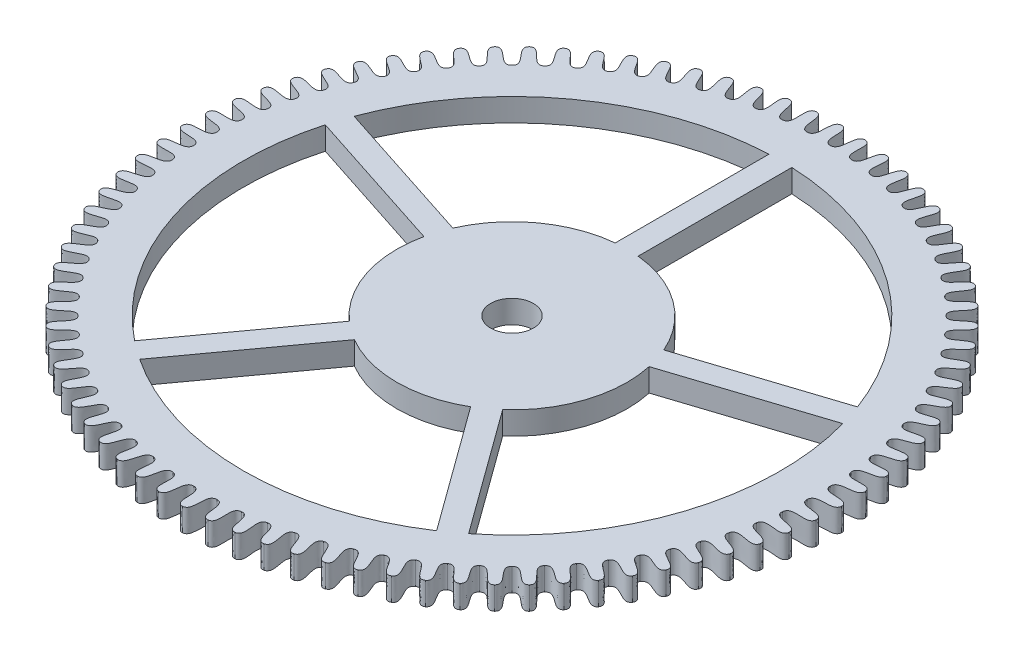
SolidWorks part; units mm, degrees
ref_plane "Alzado" through (0, 0, 0) normal (0, 0, 1) x (1, 0, 0)
ref_plane "Planta" through (0, 0, 0) normal (0, 1, 0) x (1, 0, 0)
ref_plane "Vista lateral" through (0, 0, 0) normal (1, 0, 0) x (0, 0, -1)
sketch "Sketch1" plane through (0, 0, 0) normal (0, 1, 0) x (1, 0, 0)
  line L0 (0, -1000) -> (0, 49000) construction
  line L1 (0, 0) -> (1869.5597, 49965.0352) construction
  circle A0 centre (0, 0) radius 4.315 construction
  circle A1 centre (0, 0) radius 4.015 construction
  spline S0 degree 3 poles (0, 4.315) (0.1353, 4.3129) (0.008, 4.0167) (0.1501, 4.0122) knots 0 0 0 0 1 1 1 1
  spline S1 degree 3 poles (0, 4.315) (-0.1353, 4.3129) (-0.008, 4.0167) (-0.1501, 4.0122) knots 0 0 0 0 1 1 1 1
  spline S2 degree 3 poles (0.3225, 4.3029) (0.4572, 4.2907) (0.3081, 4.0048) (0.4495, 3.9898) knots 0 0 0 0 1 1 1 1
  spline S3 degree 3 poles (0.3225, 4.3029) (0.1874, 4.3109) (0.2922, 4.006) (0.1501, 4.0122) knots 0 0 0 0 1 1 1 1
  spline S4 degree 3 poles (0.6431, 4.2668) (0.7765, 4.2445) (0.6066, 3.9706) (0.7464, 3.945) knots 0 0 0 0 1 1 1 1
  spline S5 degree 3 poles (0.6431, 4.2668) (0.5091, 4.2849) (0.5907, 3.973) (0.4495, 3.9898) knots 0 0 0 0 1 1 1 1
  spline S6 degree 3 poles (0.9602, 4.2068) (1.0916, 4.1746) (0.9016, 3.9142) (1.0392, 3.8782) knots 0 0 0 0 1 1 1 1
  spline S7 degree 3 poles (0.9602, 4.2068) (0.8278, 4.2348) (0.886, 3.9177) (0.7464, 3.945) knots 0 0 0 0 1 1 1 1
  spline S8 degree 3 poles (1.2719, 4.1233) (1.4005, 4.0814) (1.1916, 3.8358) (1.3261, 3.7897) knots 0 0 0 0 1 1 1 1
  spline S9 degree 3 poles (1.2719, 4.1233) (1.142, 4.1611) (1.1763, 3.8406) (1.0392, 3.8782) knots 0 0 0 0 1 1 1 1
  spline S10 degree 3 poles (1.5764, 4.0167) (1.7016, 3.9653) (1.4749, 3.7361) (1.6056, 3.68) knots 0 0 0 0 1 1 1 1
  spline S11 degree 3 poles (1.5764, 4.0167) (1.4498, 4.0642) (1.46, 3.7419) (1.3261, 3.7897) knots 0 0 0 0 1 1 1 1
  spline S12 degree 3 poles (1.8722, 3.8877) (1.9932, 3.8271) (1.75, 3.6154) (1.8761, 3.5497) knots 0 0 0 0 1 1 1 1
  spline S13 degree 3 poles (1.8722, 3.8877) (1.7494, 3.9445) (1.7356, 3.6223) (1.6056, 3.68) knots 0 0 0 0 1 1 1 1
  spline S14 degree 3 poles (2.1575, 3.7369) (2.2736, 3.6674) (2.0153, 3.4745) (2.1361, 3.3996) knots 0 0 0 0 1 1 1 1
  spline S15 degree 3 poles (2.1575, 3.7369) (2.0393, 3.8027) (2.0014, 3.4825) (1.8761, 3.5497) knots 0 0 0 0 1 1 1 1
  spline S16 degree 3 poles (2.4307, 3.5652) (2.5413, 3.4873) (2.2693, 3.3142) (2.3842, 3.2305) knots 0 0 0 0 1 1 1 1
  spline S17 degree 3 poles (2.4307, 3.5652) (2.3178, 3.6397) (2.2561, 3.3232) (2.1361, 3.3996) knots 0 0 0 0 1 1 1 1
  spline S18 degree 3 poles (2.6904, 3.3736) (2.7948, 3.2876) (2.5106, 3.1354) (2.6189, 3.0433) knots 0 0 0 0 1 1 1 1
  spline S19 degree 3 poles (2.6904, 3.3736) (2.5833, 3.4563) (2.4981, 3.1453) (2.3842, 3.2305) knots 0 0 0 0 1 1 1 1
  spline S20 degree 3 poles (2.9349, 3.1631) (3.0327, 3.0696) (2.7379, 2.939) (2.839, 2.839) knots 0 0 0 0 1 1 1 1
  spline S21 degree 3 poles (2.9349, 3.1631) (2.8344, 3.2536) (2.7262, 2.9499) (2.6189, 3.0433) knots 0 0 0 0 1 1 1 1
  spline S22 degree 3 poles (3.1631, 2.9349) (3.2536, 2.8344) (2.9499, 2.7262) (3.0433, 2.6189) knots 0 0 0 0 1 1 1 1
  spline S23 degree 3 poles (3.1631, 2.9349) (3.0696, 3.0327) (2.939, 2.7379) (2.839, 2.839) knots 0 0 0 0 1 1 1 1
  spline S24 degree 3 poles (3.3736, 2.6904) (3.4563, 2.5833) (3.1453, 2.4981) (3.2305, 2.3842) knots 0 0 0 0 1 1 1 1
  spline S25 degree 3 poles (3.3736, 2.6904) (3.2876, 2.7948) (3.1354, 2.5106) (3.0433, 2.6189) knots 0 0 0 0 1 1 1 1
  spline S26 degree 3 poles (3.5652, 2.4307) (3.6397, 2.3178) (3.3232, 2.2561) (3.3996, 2.1361) knots 0 0 0 0 1 1 1 1
  spline S27 degree 3 poles (3.5652, 2.4307) (3.4873, 2.5413) (3.3142, 2.2693) (3.2305, 2.3842) knots 0 0 0 0 1 1 1 1
  spline S28 degree 3 poles (3.7369, 2.1575) (3.8027, 2.0393) (3.4825, 2.0014) (3.5497, 1.8761) knots 0 0 0 0 1 1 1 1
  spline S29 degree 3 poles (3.7369, 2.1575) (3.6674, 2.2736) (3.4745, 2.0153) (3.3996, 2.1361) knots 0 0 0 0 1 1 1 1
  spline S30 degree 3 poles (3.8877, 1.8722) (3.9445, 1.7494) (3.6223, 1.7356) (3.68, 1.6056) knots 0 0 0 0 1 1 1 1
  spline S31 degree 3 poles (3.8877, 1.8722) (3.8271, 1.9932) (3.6154, 1.75) (3.5497, 1.8761) knots 0 0 0 0 1 1 1 1
  spline S32 degree 3 poles (4.0167, 1.5764) (4.0642, 1.4498) (3.7419, 1.46) (3.7897, 1.3261) knots 0 0 0 0 1 1 1 1
  spline S33 degree 3 poles (4.0167, 1.5764) (3.9653, 1.7016) (3.7361, 1.4749) (3.68, 1.6056) knots 0 0 0 0 1 1 1 1
  spline S34 degree 3 poles (4.1233, 1.2719) (4.1611, 1.142) (3.8406, 1.1763) (3.8782, 1.0392) knots 0 0 0 0 1 1 1 1
  spline S35 degree 3 poles (4.1233, 1.2719) (4.0814, 1.4005) (3.8358, 1.1916) (3.7897, 1.3261) knots 0 0 0 0 1 1 1 1
  spline S36 degree 3 poles (4.2068, 0.9602) (4.2348, 0.8278) (3.9177, 0.886) (3.945, 0.7464) knots 0 0 0 0 1 1 1 1
  spline S37 degree 3 poles (4.2068, 0.9602) (4.1746, 1.0916) (3.9142, 0.9016) (3.8782, 1.0392) knots 0 0 0 0 1 1 1 1
  spline S38 degree 3 poles (4.2668, 0.6431) (4.2849, 0.5091) (3.973, 0.5907) (3.9898, 0.4495) knots 0 0 0 0 1 1 1 1
  spline S39 degree 3 poles (4.2668, 0.6431) (4.2445, 0.7765) (3.9706, 0.6066) (3.945, 0.7464) knots 0 0 0 0 1 1 1 1
  spline S40 degree 3 poles (4.3029, 0.3225) (4.3109, 0.1874) (4.006, 0.2922) (4.0122, 0.1501) knots 0 0 0 0 1 1 1 1
  spline S41 degree 3 poles (4.3029, 0.3225) (4.2907, 0.4572) (4.0048, 0.3081) (3.9898, 0.4495) knots 0 0 0 0 1 1 1 1
  spline S42 degree 3 poles (4.315, 0) (4.3129, -0.1353) (4.0167, -0.008) (4.0122, -0.1501) knots 0 0 0 0 1 1 1 1
  spline S43 degree 3 poles (4.315, 0) (4.3129, 0.1353) (4.0167, 0.008) (4.0122, 0.1501) knots 0 0 0 0 1 1 1 1
  spline S44 degree 3 poles (4.3029, -0.3225) (4.2907, -0.4572) (4.0048, -0.3081) (3.9898, -0.4495) knots 0 0 0 0 1 1 1 1
  spline S45 degree 3 poles (4.3029, -0.3225) (4.3109, -0.1874) (4.006, -0.2922) (4.0122, -0.1501) knots 0 0 0 0 1 1 1 1
  spline S46 degree 3 poles (4.2668, -0.6431) (4.2445, -0.7765) (3.9706, -0.6066) (3.945, -0.7464) knots 0 0 0 0 1 1 1 1
  spline S47 degree 3 poles (4.2668, -0.6431) (4.2849, -0.5091) (3.973, -0.5907) (3.9898, -0.4495) knots 0 0 0 0 1 1 1 1
  spline S48 degree 3 poles (4.2068, -0.9602) (4.1746, -1.0916) (3.9142, -0.9016) (3.8782, -1.0392) knots 0 0 0 0 1 1 1 1
  spline S49 degree 3 poles (4.2068, -0.9602) (4.2348, -0.8278) (3.9177, -0.886) (3.945, -0.7464) knots 0 0 0 0 1 1 1 1
  spline S50 degree 3 poles (4.1233, -1.2719) (4.0814, -1.4005) (3.8358, -1.1916) (3.7897, -1.3261) knots 0 0 0 0 1 1 1 1
  spline S51 degree 3 poles (4.1233, -1.2719) (4.1611, -1.142) (3.8406, -1.1763) (3.8782, -1.0392) knots 0 0 0 0 1 1 1 1
  spline S52 degree 3 poles (4.0167, -1.5764) (3.9653, -1.7016) (3.7361, -1.4749) (3.68, -1.6056) knots 0 0 0 0 1 1 1 1
  spline S53 degree 3 poles (4.0167, -1.5764) (4.0642, -1.4498) (3.7419, -1.46) (3.7897, -1.3261) knots 0 0 0 0 1 1 1 1
  spline S54 degree 3 poles (3.8877, -1.8722) (3.8271, -1.9932) (3.6154, -1.75) (3.5497, -1.8761) knots 0 0 0 0 1 1 1 1
  spline S55 degree 3 poles (3.8877, -1.8722) (3.9445, -1.7494) (3.6223, -1.7356) (3.68, -1.6056) knots 0 0 0 0 1 1 1 1
  spline S56 degree 3 poles (3.7369, -2.1575) (3.6674, -2.2736) (3.4745, -2.0153) (3.3996, -2.1361) knots 0 0 0 0 1 1 1 1
  spline S57 degree 3 poles (3.7369, -2.1575) (3.8027, -2.0393) (3.4825, -2.0014) (3.5497, -1.8761) knots 0 0 0 0 1 1 1 1
  spline S58 degree 3 poles (3.5652, -2.4307) (3.4873, -2.5413) (3.3142, -2.2693) (3.2305, -2.3842) knots 0 0 0 0 1 1 1 1
  spline S59 degree 3 poles (3.5652, -2.4307) (3.6397, -2.3178) (3.3232, -2.2561) (3.3996, -2.1361) knots 0 0 0 0 1 1 1 1
  spline S60 degree 3 poles (3.3736, -2.6904) (3.2876, -2.7948) (3.1354, -2.5106) (3.0433, -2.6189) knots 0 0 0 0 1 1 1 1
  spline S61 degree 3 poles (3.3736, -2.6904) (3.4563, -2.5833) (3.1453, -2.4981) (3.2305, -2.3842) knots 0 0 0 0 1 1 1 1
  spline S62 degree 3 poles (3.1631, -2.9349) (3.0696, -3.0327) (2.939, -2.7379) (2.839, -2.839) knots 0 0 0 0 1 1 1 1
  spline S63 degree 3 poles (3.1631, -2.9349) (3.2536, -2.8344) (2.9499, -2.7262) (3.0433, -2.6189) knots 0 0 0 0 1 1 1 1
  spline S64 degree 3 poles (2.9349, -3.1631) (2.8344, -3.2536) (2.7262, -2.9499) (2.6189, -3.0433) knots 0 0 0 0 1 1 1 1
  spline S65 degree 3 poles (2.9349, -3.1631) (3.0327, -3.0696) (2.7379, -2.939) (2.839, -2.839) knots 0 0 0 0 1 1 1 1
  spline S66 degree 3 poles (2.6904, -3.3736) (2.5833, -3.4563) (2.4981, -3.1453) (2.3842, -3.2305) knots 0 0 0 0 1 1 1 1
  spline S67 degree 3 poles (2.6904, -3.3736) (2.7948, -3.2876) (2.5106, -3.1354) (2.6189, -3.0433) knots 0 0 0 0 1 1 1 1
  spline S68 degree 3 poles (2.4307, -3.5652) (2.3178, -3.6397) (2.2561, -3.3232) (2.1361, -3.3996) knots 0 0 0 0 1 1 1 1
  spline S69 degree 3 poles (2.4307, -3.5652) (2.5413, -3.4873) (2.2693, -3.3142) (2.3842, -3.2305) knots 0 0 0 0 1 1 1 1
  spline S70 degree 3 poles (2.1575, -3.7369) (2.0393, -3.8027) (2.0014, -3.4825) (1.8761, -3.5497) knots 0 0 0 0 1 1 1 1
  spline S71 degree 3 poles (2.1575, -3.7369) (2.2736, -3.6674) (2.0153, -3.4745) (2.1361, -3.3996) knots 0 0 0 0 1 1 1 1
  spline S72 degree 3 poles (1.8722, -3.8877) (1.7494, -3.9445) (1.7356, -3.6223) (1.6056, -3.68) knots 0 0 0 0 1 1 1 1
  spline S73 degree 3 poles (1.8722, -3.8877) (1.9932, -3.8271) (1.75, -3.6154) (1.8761, -3.5497) knots 0 0 0 0 1 1 1 1
  spline S74 degree 3 poles (1.5764, -4.0167) (1.4498, -4.0642) (1.46, -3.7419) (1.3261, -3.7897) knots 0 0 0 0 1 1 1 1
  spline S75 degree 3 poles (1.5764, -4.0167) (1.7016, -3.9653) (1.4749, -3.7361) (1.6056, -3.68) knots 0 0 0 0 1 1 1 1
  spline S76 degree 3 poles (1.2719, -4.1233) (1.142, -4.1611) (1.1763, -3.8406) (1.0392, -3.8782) knots 0 0 0 0 1 1 1 1
  spline S77 degree 3 poles (1.2719, -4.1233) (1.4005, -4.0814) (1.1916, -3.8358) (1.3261, -3.7897) knots 0 0 0 0 1 1 1 1
  spline S78 degree 3 poles (0.9602, -4.2068) (0.8278, -4.2348) (0.886, -3.9177) (0.7464, -3.945) knots 0 0 0 0 1 1 1 1
  spline S79 degree 3 poles (0.9602, -4.2068) (1.0916, -4.1746) (0.9016, -3.9142) (1.0392, -3.8782) knots 0 0 0 0 1 1 1 1
  spline S80 degree 3 poles (0.6431, -4.2668) (0.5091, -4.2849) (0.5907, -3.973) (0.4495, -3.9898) knots 0 0 0 0 1 1 1 1
  spline S81 degree 3 poles (0.6431, -4.2668) (0.7765, -4.2445) (0.6066, -3.9706) (0.7464, -3.945) knots 0 0 0 0 1 1 1 1
  spline S82 degree 3 poles (0.3225, -4.3029) (0.1874, -4.3109) (0.2922, -4.006) (0.1501, -4.0122) knots 0 0 0 0 1 1 1 1
  spline S83 degree 3 poles (0.3225, -4.3029) (0.4572, -4.2907) (0.3081, -4.0048) (0.4495, -3.9898) knots 0 0 0 0 1 1 1 1
  spline S84 degree 3 poles (0, -4.315) (-0.1353, -4.3129) (-0.008, -4.0167) (-0.1501, -4.0122) knots 0 0 0 0 1 1 1 1
  spline S85 degree 3 poles (0, -4.315) (0.1353, -4.3129) (0.008, -4.0167) (0.1501, -4.0122) knots 0 0 0 0 1 1 1 1
  spline S86 degree 3 poles (-0.3225, -4.3029) (-0.4572, -4.2907) (-0.3081, -4.0048) (-0.4495, -3.9898) knots 0 0 0 0 1 1 1 1
  spline S87 degree 3 poles (-0.3225, -4.3029) (-0.1874, -4.3109) (-0.2922, -4.006) (-0.1501, -4.0122) knots 0 0 0 0 1 1 1 1
  spline S88 degree 3 poles (-0.6431, -4.2668) (-0.7765, -4.2445) (-0.6066, -3.9706) (-0.7464, -3.945) knots 0 0 0 0 1 1 1 1
  spline S89 degree 3 poles (-0.6431, -4.2668) (-0.5091, -4.2849) (-0.5907, -3.973) (-0.4495, -3.9898) knots 0 0 0 0 1 1 1 1
  spline S90 degree 3 poles (-0.9602, -4.2068) (-1.0916, -4.1746) (-0.9016, -3.9142) (-1.0392, -3.8782) knots 0 0 0 0 1 1 1 1
  spline S91 degree 3 poles (-0.9602, -4.2068) (-0.8278, -4.2348) (-0.886, -3.9177) (-0.7464, -3.945) knots 0 0 0 0 1 1 1 1
  spline S92 degree 3 poles (-1.2719, -4.1233) (-1.4005, -4.0814) (-1.1916, -3.8358) (-1.3261, -3.7897) knots 0 0 0 0 1 1 1 1
  spline S93 degree 3 poles (-1.2719, -4.1233) (-1.142, -4.1611) (-1.1763, -3.8406) (-1.0392, -3.8782) knots 0 0 0 0 1 1 1 1
  spline S94 degree 3 poles (-1.5764, -4.0167) (-1.7016, -3.9653) (-1.4749, -3.7361) (-1.6056, -3.68) knots 0 0 0 0 1 1 1 1
  spline S95 degree 3 poles (-1.5764, -4.0167) (-1.4498, -4.0642) (-1.46, -3.7419) (-1.3261, -3.7897) knots 0 0 0 0 1 1 1 1
  spline S96 degree 3 poles (-1.8722, -3.8877) (-1.9932, -3.8271) (-1.75, -3.6154) (-1.8761, -3.5497) knots 0 0 0 0 1 1 1 1
  spline S97 degree 3 poles (-1.8722, -3.8877) (-1.7494, -3.9445) (-1.7356, -3.6223) (-1.6056, -3.68) knots 0 0 0 0 1 1 1 1
  spline S98 degree 3 poles (-2.1575, -3.7369) (-2.2736, -3.6674) (-2.0153, -3.4745) (-2.1361, -3.3996) knots 0 0 0 0 1 1 1 1
  spline S99 degree 3 poles (-2.1575, -3.7369) (-2.0393, -3.8027) (-2.0014, -3.4825) (-1.8761, -3.5497) knots 0 0 0 0 1 1 1 1
  spline S100 degree 3 poles (-2.4307, -3.5652) (-2.5413, -3.4873) (-2.2693, -3.3142) (-2.3842, -3.2305) knots 0 0 0 0 1 1 1 1
  spline S101 degree 3 poles (-2.4307, -3.5652) (-2.3178, -3.6397) (-2.2561, -3.3232) (-2.1361, -3.3996) knots 0 0 0 0 1 1 1 1
  spline S102 degree 3 poles (-2.6904, -3.3736) (-2.7948, -3.2876) (-2.5106, -3.1354) (-2.6189, -3.0433) knots 0 0 0 0 1 1 1 1
  spline S103 degree 3 poles (-2.6904, -3.3736) (-2.5833, -3.4563) (-2.4981, -3.1453) (-2.3842, -3.2305) knots 0 0 0 0 1 1 1 1
  spline S104 degree 3 poles (-2.9349, -3.1631) (-3.0327, -3.0696) (-2.7379, -2.939) (-2.839, -2.839) knots 0 0 0 0 1 1 1 1
  spline S105 degree 3 poles (-2.9349, -3.1631) (-2.8344, -3.2536) (-2.7262, -2.9499) (-2.6189, -3.0433) knots 0 0 0 0 1 1 1 1
  spline S106 degree 3 poles (-3.1631, -2.9349) (-3.2536, -2.8344) (-2.9499, -2.7262) (-3.0433, -2.6189) knots 0 0 0 0 1 1 1 1
  spline S107 degree 3 poles (-3.1631, -2.9349) (-3.0696, -3.0327) (-2.939, -2.7379) (-2.839, -2.839) knots 0 0 0 0 1 1 1 1
  spline S108 degree 3 poles (-3.3736, -2.6904) (-3.4563, -2.5833) (-3.1453, -2.4981) (-3.2305, -2.3842) knots 0 0 0 0 1 1 1 1
  spline S109 degree 3 poles (-3.3736, -2.6904) (-3.2876, -2.7948) (-3.1354, -2.5106) (-3.0433, -2.6189) knots 0 0 0 0 1 1 1 1
  spline S110 degree 3 poles (-3.5652, -2.4307) (-3.6397, -2.3178) (-3.3232, -2.2561) (-3.3996, -2.1361) knots 0 0 0 0 1 1 1 1
  spline S111 degree 3 poles (-3.5652, -2.4307) (-3.4873, -2.5413) (-3.3142, -2.2693) (-3.2305, -2.3842) knots 0 0 0 0 1 1 1 1
  spline S112 degree 3 poles (-3.7369, -2.1575) (-3.8027, -2.0393) (-3.4825, -2.0014) (-3.5497, -1.8761) knots 0 0 0 0 1 1 1 1
  spline S113 degree 3 poles (-3.7369, -2.1575) (-3.6674, -2.2736) (-3.4745, -2.0153) (-3.3996, -2.1361) knots 0 0 0 0 1 1 1 1
  spline S114 degree 3 poles (-3.8877, -1.8722) (-3.9445, -1.7494) (-3.6223, -1.7356) (-3.68, -1.6056) knots 0 0 0 0 1 1 1 1
  spline S115 degree 3 poles (-3.8877, -1.8722) (-3.8271, -1.9932) (-3.6154, -1.75) (-3.5497, -1.8761) knots 0 0 0 0 1 1 1 1
  spline S116 degree 3 poles (-4.0167, -1.5764) (-4.0642, -1.4498) (-3.7419, -1.46) (-3.7897, -1.3261) knots 0 0 0 0 1 1 1 1
  spline S117 degree 3 poles (-4.0167, -1.5764) (-3.9653, -1.7016) (-3.7361, -1.4749) (-3.68, -1.6056) knots 0 0 0 0 1 1 1 1
  spline S118 degree 3 poles (-4.1233, -1.2719) (-4.1611, -1.142) (-3.8406, -1.1763) (-3.8782, -1.0392) knots 0 0 0 0 1 1 1 1
  spline S119 degree 3 poles (-4.1233, -1.2719) (-4.0814, -1.4005) (-3.8358, -1.1916) (-3.7897, -1.3261) knots 0 0 0 0 1 1 1 1
  spline S120 degree 3 poles (-4.2068, -0.9602) (-4.2348, -0.8278) (-3.9177, -0.886) (-3.945, -0.7464) knots 0 0 0 0 1 1 1 1
  spline S121 degree 3 poles (-4.2068, -0.9602) (-4.1746, -1.0916) (-3.9142, -0.9016) (-3.8782, -1.0392) knots 0 0 0 0 1 1 1 1
  spline S122 degree 3 poles (-4.2668, -0.6431) (-4.2849, -0.5091) (-3.973, -0.5907) (-3.9898, -0.4495) knots 0 0 0 0 1 1 1 1
  spline S123 degree 3 poles (-4.2668, -0.6431) (-4.2445, -0.7765) (-3.9706, -0.6066) (-3.945, -0.7464) knots 0 0 0 0 1 1 1 1
  spline S124 degree 3 poles (-4.3029, -0.3225) (-4.3109, -0.1874) (-4.006, -0.2922) (-4.0122, -0.1501) knots 0 0 0 0 1 1 1 1
  spline S125 degree 3 poles (-4.3029, -0.3225) (-4.2907, -0.4572) (-4.0048, -0.3081) (-3.9898, -0.4495) knots 0 0 0 0 1 1 1 1
  spline S126 degree 3 poles (-4.315, 0) (-4.3129, 0.1353) (-4.0167, 0.008) (-4.0122, 0.1501) knots 0 0 0 0 1 1 1 1
  spline S127 degree 3 poles (-4.315, 0) (-4.3129, -0.1353) (-4.0167, -0.008) (-4.0122, -0.1501) knots 0 0 0 0 1 1 1 1
  spline S128 degree 3 poles (-4.3029, 0.3225) (-4.2907, 0.4572) (-4.0048, 0.3081) (-3.9898, 0.4495) knots 0 0 0 0 1 1 1 1
  spline S129 degree 3 poles (-4.3029, 0.3225) (-4.3109, 0.1874) (-4.006, 0.2922) (-4.0122, 0.1501) knots 0 0 0 0 1 1 1 1
  spline S130 degree 3 poles (-4.2668, 0.6431) (-4.2445, 0.7765) (-3.9706, 0.6066) (-3.945, 0.7464) knots 0 0 0 0 1 1 1 1
  spline S131 degree 3 poles (-4.2668, 0.6431) (-4.2849, 0.5091) (-3.973, 0.5907) (-3.9898, 0.4495) knots 0 0 0 0 1 1 1 1
  spline S132 degree 3 poles (-4.2068, 0.9602) (-4.1746, 1.0916) (-3.9142, 0.9016) (-3.8782, 1.0392) knots 0 0 0 0 1 1 1 1
  spline S133 degree 3 poles (-4.2068, 0.9602) (-4.2348, 0.8278) (-3.9177, 0.886) (-3.945, 0.7464) knots 0 0 0 0 1 1 1 1
  spline S134 degree 3 poles (-4.1233, 1.2719) (-4.0814, 1.4005) (-3.8358, 1.1916) (-3.7897, 1.3261) knots 0 0 0 0 1 1 1 1
  spline S135 degree 3 poles (-4.1233, 1.2719) (-4.1611, 1.142) (-3.8406, 1.1763) (-3.8782, 1.0392) knots 0 0 0 0 1 1 1 1
  spline S136 degree 3 poles (-4.0167, 1.5764) (-3.9653, 1.7016) (-3.7361, 1.4749) (-3.68, 1.6056) knots 0 0 0 0 1 1 1 1
  spline S137 degree 3 poles (-4.0167, 1.5764) (-4.0642, 1.4498) (-3.7419, 1.46) (-3.7897, 1.3261) knots 0 0 0 0 1 1 1 1
  spline S138 degree 3 poles (-3.8877, 1.8722) (-3.8271, 1.9932) (-3.6154, 1.75) (-3.5497, 1.8761) knots 0 0 0 0 1 1 1 1
  spline S139 degree 3 poles (-3.8877, 1.8722) (-3.9445, 1.7494) (-3.6223, 1.7356) (-3.68, 1.6056) knots 0 0 0 0 1 1 1 1
  spline S140 degree 3 poles (-3.7369, 2.1575) (-3.6674, 2.2736) (-3.4745, 2.0153) (-3.3996, 2.1361) knots 0 0 0 0 1 1 1 1
  spline S141 degree 3 poles (-3.7369, 2.1575) (-3.8027, 2.0393) (-3.4825, 2.0014) (-3.5497, 1.8761) knots 0 0 0 0 1 1 1 1
  spline S142 degree 3 poles (-3.5652, 2.4307) (-3.4873, 2.5413) (-3.3142, 2.2693) (-3.2305, 2.3842) knots 0 0 0 0 1 1 1 1
  spline S143 degree 3 poles (-3.5652, 2.4307) (-3.6397, 2.3178) (-3.3232, 2.2561) (-3.3996, 2.1361) knots 0 0 0 0 1 1 1 1
  spline S144 degree 3 poles (-3.3736, 2.6904) (-3.2876, 2.7948) (-3.1354, 2.5106) (-3.0433, 2.6189) knots 0 0 0 0 1 1 1 1
  spline S145 degree 3 poles (-3.3736, 2.6904) (-3.4563, 2.5833) (-3.1453, 2.4981) (-3.2305, 2.3842) knots 0 0 0 0 1 1 1 1
  spline S146 degree 3 poles (-3.1631, 2.9349) (-3.0696, 3.0327) (-2.939, 2.7379) (-2.839, 2.839) knots 0 0 0 0 1 1 1 1
  spline S147 degree 3 poles (-3.1631, 2.9349) (-3.2536, 2.8344) (-2.9499, 2.7262) (-3.0433, 2.6189) knots 0 0 0 0 1 1 1 1
  spline S148 degree 3 poles (-2.9349, 3.1631) (-2.8344, 3.2536) (-2.7262, 2.9499) (-2.6189, 3.0433) knots 0 0 0 0 1 1 1 1
  spline S149 degree 3 poles (-2.9349, 3.1631) (-3.0327, 3.0696) (-2.7379, 2.939) (-2.839, 2.839) knots 0 0 0 0 1 1 1 1
  spline S150 degree 3 poles (-2.6904, 3.3736) (-2.5833, 3.4563) (-2.4981, 3.1453) (-2.3842, 3.2305) knots 0 0 0 0 1 1 1 1
  spline S151 degree 3 poles (-2.6904, 3.3736) (-2.7948, 3.2876) (-2.5106, 3.1354) (-2.6189, 3.0433) knots 0 0 0 0 1 1 1 1
  spline S152 degree 3 poles (-2.4307, 3.5652) (-2.3178, 3.6397) (-2.2561, 3.3232) (-2.1361, 3.3996) knots 0 0 0 0 1 1 1 1
  spline S153 degree 3 poles (-2.4307, 3.5652) (-2.5413, 3.4873) (-2.2693, 3.3142) (-2.3842, 3.2305) knots 0 0 0 0 1 1 1 1
  spline S154 degree 3 poles (-2.1575, 3.7369) (-2.0393, 3.8027) (-2.0014, 3.4825) (-1.8761, 3.5497) knots 0 0 0 0 1 1 1 1
  spline S155 degree 3 poles (-2.1575, 3.7369) (-2.2736, 3.6674) (-2.0153, 3.4745) (-2.1361, 3.3996) knots 0 0 0 0 1 1 1 1
  spline S156 degree 3 poles (-1.8722, 3.8877) (-1.7494, 3.9445) (-1.7356, 3.6223) (-1.6056, 3.68) knots 0 0 0 0 1 1 1 1
  spline S157 degree 3 poles (-1.8722, 3.8877) (-1.9932, 3.8271) (-1.75, 3.6154) (-1.8761, 3.5497) knots 0 0 0 0 1 1 1 1
  spline S158 degree 3 poles (-1.5764, 4.0167) (-1.4498, 4.0642) (-1.46, 3.7419) (-1.3261, 3.7897) knots 0 0 0 0 1 1 1 1
  spline S159 degree 3 poles (-1.5764, 4.0167) (-1.7016, 3.9653) (-1.4749, 3.7361) (-1.6056, 3.68) knots 0 0 0 0 1 1 1 1
  spline S160 degree 3 poles (-1.2719, 4.1233) (-1.142, 4.1611) (-1.1763, 3.8406) (-1.0392, 3.8782) knots 0 0 0 0 1 1 1 1
  spline S161 degree 3 poles (-1.2719, 4.1233) (-1.4005, 4.0814) (-1.1916, 3.8358) (-1.3261, 3.7897) knots 0 0 0 0 1 1 1 1
  spline S162 degree 3 poles (-0.9602, 4.2068) (-0.8278, 4.2348) (-0.886, 3.9177) (-0.7464, 3.945) knots 0 0 0 0 1 1 1 1
  spline S163 degree 3 poles (-0.9602, 4.2068) (-1.0916, 4.1746) (-0.9016, 3.9142) (-1.0392, 3.8782) knots 0 0 0 0 1 1 1 1
  spline S164 degree 3 poles (-0.6431, 4.2668) (-0.5091, 4.2849) (-0.5907, 3.973) (-0.4495, 3.9898) knots 0 0 0 0 1 1 1 1
  spline S165 degree 3 poles (-0.6431, 4.2668) (-0.7765, 4.2445) (-0.6066, 3.9706) (-0.7464, 3.945) knots 0 0 0 0 1 1 1 1
  spline S166 degree 3 poles (-0.3225, 4.3029) (-0.1874, 4.3109) (-0.2922, 4.006) (-0.1501, 4.0122) knots 0 0 0 0 1 1 1 1
  spline S167 degree 3 poles (-0.3225, 4.3029) (-0.4572, 4.2907) (-0.3081, 4.0048) (-0.4495, 3.9898) knots 0 0 0 0 1 1 1 1
  point P4 (0, 4.315)
  point P9 (0.1501, 4.0122)
  point P264 (0, 0)
  point P267 (0, 0)
  dimension "D1" = 8.63
  dimension "D2" = 0.3
  dimension "D3" = 2.143
extrude "Boss-Extrude1 (84 teeth)" add sketch "Sketch1" along normal blind 0.3
sketch "Sketch3" plane through (0, 0, 0) normal (0, 1, 0) x (1, 0, 0)
  line L0 (0, -1000) -> (0, 49000) construction
  line L1 (0.15, -999.8847) -> (0.15, 49000.1153) construction
  line L2 (-0.15, -999.6818) -> (-0.15, 49000.3182) construction
  line L3 (-0.15, 3.5118) -> (-0.15, 1.5005)
  line L4 (3.2936, 1.2279) -> (1.3807, 0.6063)
  line L5 (0.15, 1.5005) -> (0.15, 3.5118)
  line L6 (1.4734, 0.321) -> (3.3863, 0.9425)
  line L7 (2.1855, -2.7529) -> (1.0033, -1.1258)
  line L8 (0.7606, -1.3021) -> (1.9428, -2.9293)
  line L9 (-1.9428, -2.9293) -> (-0.7606, -1.3021)
  line L10 (-1.0033, -1.1258) -> (-2.1855, -2.7529)
  line L11 (-3.3863, 0.9425) -> (-1.4734, 0.321)
  line L12 (-1.3807, 0.6063) -> (-3.2936, 1.2279)
  arc A0 (-0.15, 3.5118) -> (-3.2936, 1.2279) centre (0, 0) ccw
  arc A1 (-0.15, 1.5005) -> (-1.3807, 0.6063) centre (0, 0) ccw
  arc A2 (-3.3863, 0.9425) -> (-2.1855, -2.7529) centre (0, 0) ccw
  arc A3 (-1.4734, 0.321) -> (-1.0033, -1.1258) centre (0, 0) ccw
  arc A4 (1.3807, 0.6063) -> (0.15, 1.5005) centre (0, 0) ccw
  arc A5 (3.2936, 1.2279) -> (0.15, 3.5118) centre (0, 0) ccw
  arc A6 (1.0033, -1.1258) -> (1.4734, 0.321) centre (0, 0) ccw
  arc A7 (-0.7606, -1.3021) -> (0.7606, -1.3021) centre (0, 0) ccw
  arc A8 (-1.9428, -2.9293) -> (1.9428, -2.9293) centre (0, 0) ccw
  arc A9 (2.1855, -2.7529) -> (3.3863, 0.9425) centre (0, 0) ccw
  point P32 (0, 0)
  dimension "D3" = 7.03
  dimension "D4" = 3.016
  dimension "D1" = 0.15
  dimension "D2" = 0.15
  dimension "D5" = 5
extrude "Cut-Extrude2" cut sketch "Sketch3" along normal up to next
sketch "Sketch4" plane through (0, 0, 0) normal (0, 1, 0) x (1, 0, 0)
  circle A0 centre (0, 0) radius 0.28
  dimension "D1" = 0.56
extrude "Cut-Extrude3" cut sketch "Sketch4" along normal up to next
